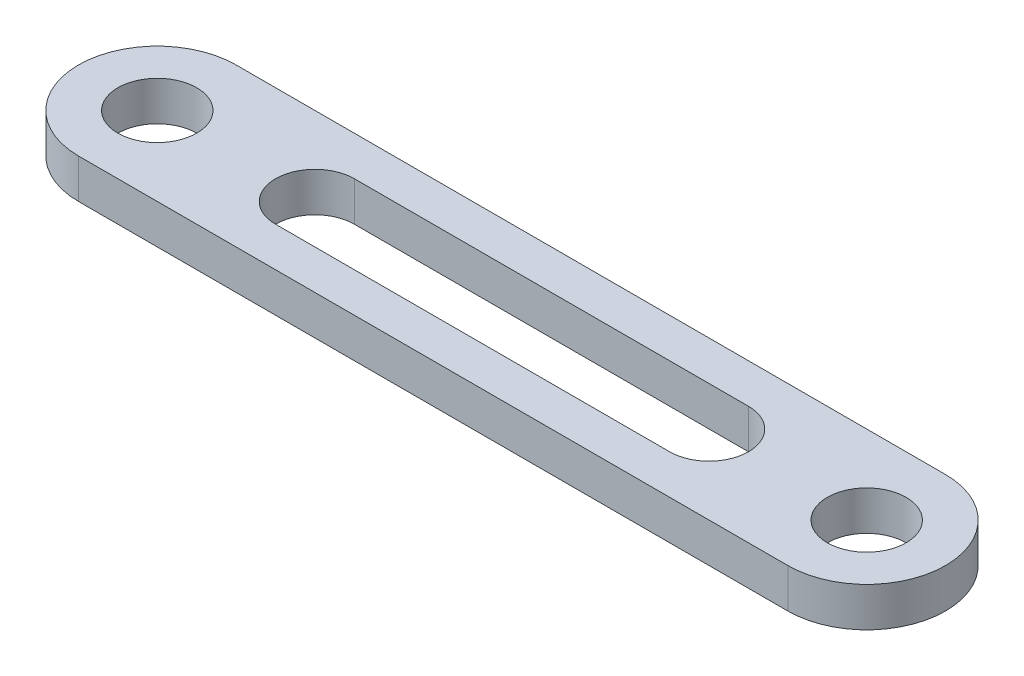
SolidWorks part; units mm, degrees
ref_plane "Front Plane" through (0, 0, 0) normal (0, 0, 1) x (1, 0, 0)
ref_plane "Top Plane" through (0, 0, 0) normal (0, 1, 0) x (1, 0, 0)
ref_plane "Right Plane" through (0, 0, 0) normal (1, 0, 0) x (0, 0, -1)
sketch "Sketch1" plane through (0, 0, 0) normal (0, 1, 0) x (1, 0, 0)
  line L0 (0, 0) -> (90, 0) construction
  line L1 (0, 10) -> (90, 10)
  line L2 (0, -10) -> (90, -10)
  line L3 (20, 0) -> (70, 0) construction
  line L4 (20, 5) -> (70, 5)
  line L5 (20, -5) -> (70, -5)
  arc A0 (0, 10) -> (0, -10) centre (0, 0) ccw
  arc A1 (90, -10) -> (90, 10) centre (90, 0) ccw
  arc A2 (20, 5) -> (20, -5) centre (20, 0) ccw
  arc A3 (70, -5) -> (70, 5) centre (70, 0) ccw
  circle A4 centre (0, 0) radius 5
  circle A5 centre (90, 0) radius 5
  point P3 (45, 0)
  point P10 (45, 0)
  dimension "D3" = 5
  dimension "D4" = 10
  dimension "D5" = 10
  dimension "D6" = 10
  dimension "D1" = 90
  dimension "D2" = 50
extrude "Boss-Extrude1" add sketch "Sketch1" along normal blind 5
